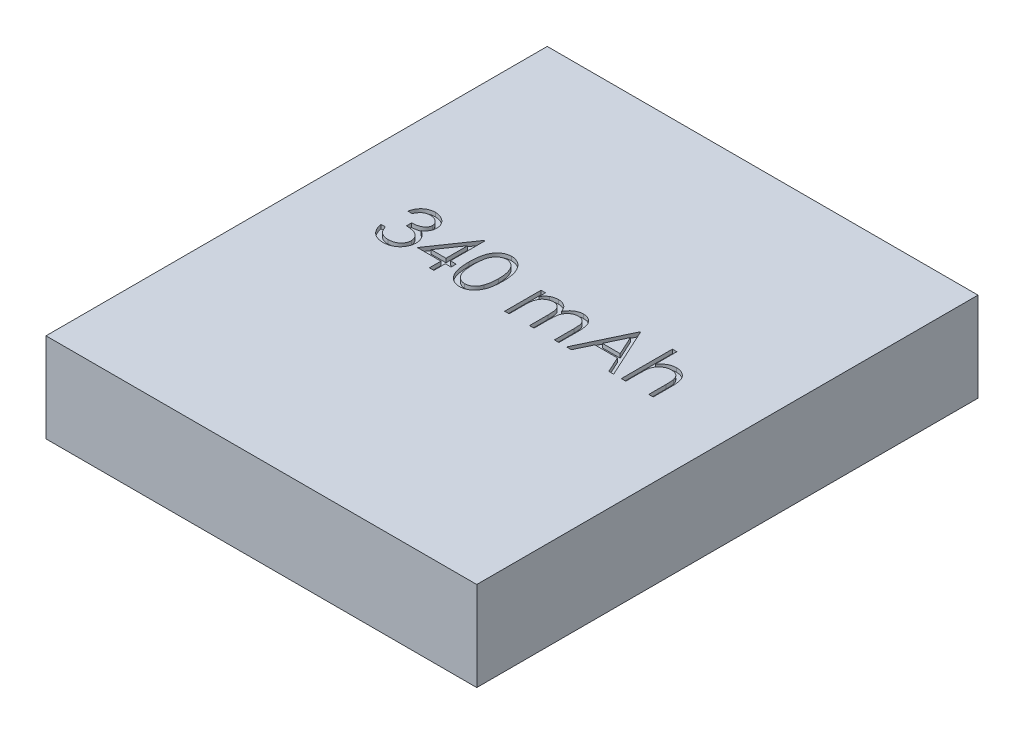
SolidWorks part; units mm, degrees
ref_plane "Front Plane" through (0, 0, 0) normal (0, 0, 1) x (1, 0, 0)
ref_plane "Top Plane" through (0, 0, 0) normal (0, 1, 0) x (1, 0, 0)
ref_plane "Right Plane" through (0, 0, 0) normal (1, 0, 0) x (0, 0, -1)
sketch "Sketch1" plane through (0, 0, 0) normal (0, 1, 0) x (1, 0, 0)
  line L1 (13.75, -16) -> (-13.75, -16)
  line L2 (13.75, -16) -> (13.75, 16)
  line L3 (13.75, 16) -> (-13.75, 16)
  line L4 (-13.75, -16) -> (-13.75, 16)
  line L5 (13.75, -16) -> (-13.75, 16) construction
  line L6 (13.75, 16) -> (-13.75, -16) construction
  point P0 (0, 0)
  dimension "D1" = 27.5
  dimension "D2" = 32
extrude "Boss-Extrude1" add sketch "Sketch1" along normal blind 5.7
sketch "Sketch2" plane through (0, 5.7, 0) normal (0, 1, 0) x (1, 0, 0)
  line L0 (11.5145, 0) -> (-11.5145, 0) construction
  text T0 "340 mAh"
  point P4 (0, 0)
extrude "Cut-Extrude1" cut sketch "Sketch2" against normal blind 0.254
